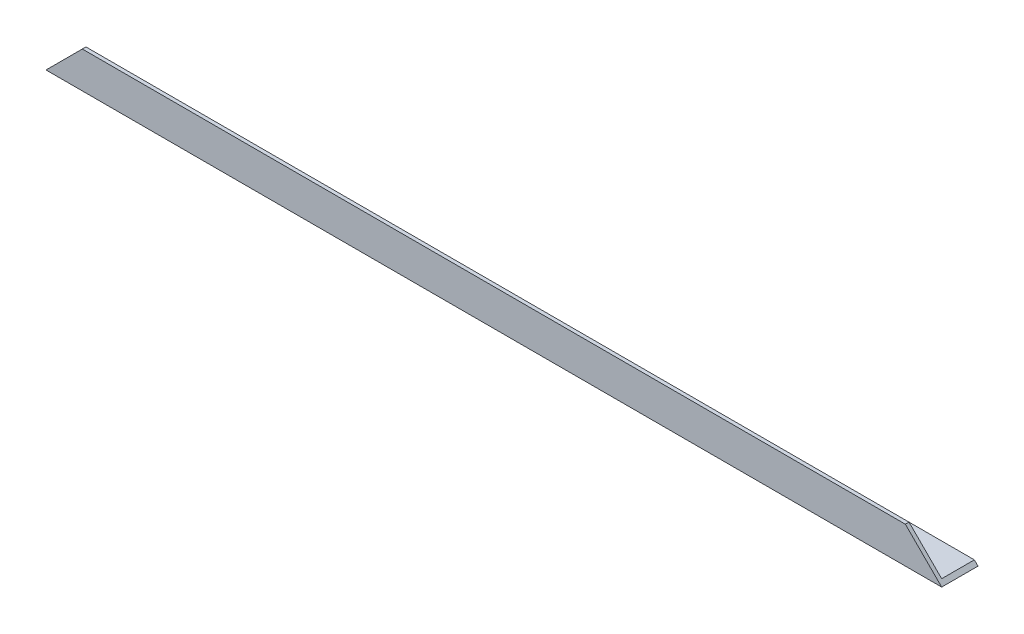
SolidWorks part; units mm, degrees
ref_plane "Спереди" through (0, 0, 0) normal (0, 0, 1) x (1, 0, 0)
ref_plane "Сверху" through (0, 0, 0) normal (0, 1, 0) x (1, 0, 0)
ref_plane "Справа" through (0, 0, 0) normal (1, 0, 0) x (0, 0, -1)
sketch "Эскиз1" plane through (0, 0, 0) normal (1, 0, 0) x (0, 0, -1)
  line L0 (0, 0) -> (0, 15)
  line L1 (0, 15) -> (1.5, 15)
  line L2 (1.5, 15) -> (1.5, 1.5)
  line L3 (1.5, 1.5) -> (15, 1.5)
  line L4 (15, 1.5) -> (15, 0)
  line L5 (15, 0) -> (0, 0)
  dimension "D1" = 15
  dimension "D2" = 15
  dimension "D3" = 1.5
  dimension "D4" = 1.5
extrude "Бобышка-Вытянуть1" add sketch "Эскиз1" along normal blind 370
sketch "Эскиз2" plane through (0, 0, 0) normal (0, 0, 1) x (1, 0, 0)
  line L3 (0, 0) -> (22.7574, 22.7574)
  line L4 (22.7574, 22.7574) -> (0, 22.7574)
  line L5 (0, 22.7574) -> (0, 0)
ref_plane "Плоскость1" through (185, 0, 0) normal (-1, 0, 0) x (0, 0, 1)
extrude "Вырез-Вытянуть1" cut sketch "Эскиз2" against normal through all
mirror "Зеркальное отражение1" about plane through (185, 0, 0) normal (-1, 0, 0) of "Вырез-Вытянуть1"
